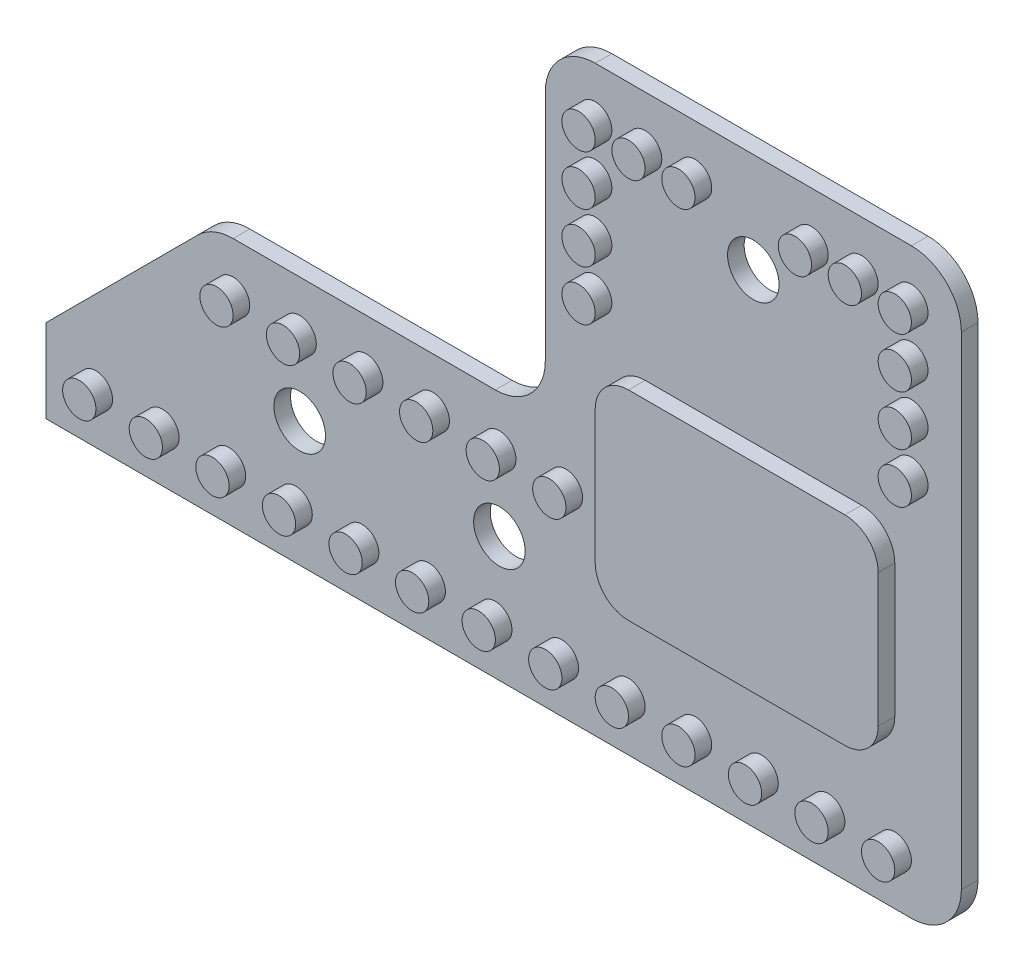
SolidWorks part; units mm, degrees
ref_plane "Front Plane" through (0, 0, 0) normal (0, 0, 1) x (1, 0, 0)
ref_plane "Top Plane" through (0, 0, 0) normal (0, 1, 0) x (1, 0, 0)
ref_plane "Right Plane" through (0, 0, 0) normal (1, 0, 0) x (0, 0, -1)
sketch "Sketch1" plane through (0, 0, 0) normal (0, 0, 1) x (1, 0, 0)
  line L0 (-36, 29) -> (-36, 12) construction
  line L1 (-41, 3) -> (-96, 3)
  line L2 (-41, 3) -> (-41, 38)
  line L3 (-41, 38) -> (-96, 38)
  line L4 (-96, 3) -> (-96, 8)
  line L5 (-40, 43) -> (-50, 43) construction
  line L6 (-96, 8) -> (-86, 18)
  line L7 (-96, 38) -> (-66, 38)
  line L8 (-96, 38) -> (-96, 18)
  line L9 (-86, 18) -> (-66, 18)
  line L10 (-66, 38) -> (-66, 18)
  line L11 (-47, 11) -> (-60, 11)
  line L12 (-45, 13) -> (-45, 21)
  line L13 (-47, 23) -> (-60, 23)
  line L14 (-62, 13) -> (-62, 21)
  line L15 (-80.7574, 15) -> (-80.7574, 6) construction
  arc A0 (-47, 23) -> (-45, 21) centre (-47, 21) cw
  arc A1 (-47, 11) -> (-45, 13) centre (-47, 13) ccw
  arc A2 (-62, 13) -> (-60, 11) centre (-60, 13) ccw
  arc A3 (-62, 21) -> (-60, 23) centre (-60, 21) cw
  circle A4 centre (-63, 35) radius 1
  circle A5 centre (-44, 35) radius 1
  circle A6 centre (-47, 35) radius 1
  circle A7 centre (-50, 35) radius 1
  circle A8 centre (-44, 32) radius 1
  circle A9 centre (-44, 29) radius 1
  circle A10 centre (-44, 26) radius 1
  circle A11 centre (-60, 35) radius 1
  circle A12 centre (-57, 35) radius 1
  circle A13 centre (-63, 32) radius 1
  circle A14 centre (-63, 29) radius 1
  circle A15 centre (-63, 26) radius 1
  circle A16 centre (-84.7574, 15) radius 1
  circle A17 centre (-80.7574, 15) radius 1
  circle A18 centre (-76.7574, 15) radius 1
  circle A19 centre (-72.7574, 15) radius 1
  circle A20 centre (-68.7574, 15) radius 1
  circle A21 centre (-64.7574, 15) radius 1
  circle A22 centre (-93, 6) radius 1
  circle A23 centre (-89, 6) radius 1
  circle A24 centre (-85, 6) radius 1
  circle A25 centre (-81, 6) radius 1
  circle A26 centre (-77, 6) radius 1
  circle A27 centre (-73, 6) radius 1
  circle A28 centre (-69, 6) radius 1
  circle A29 centre (-65, 6) radius 1
  circle A30 centre (-61, 6) radius 1
  circle A31 centre (-57, 6) radius 1
  circle A32 centre (-53, 6) radius 1
  circle A33 centre (-49, 6) radius 1
  circle A34 centre (-45, 6) radius 1
  circle A35 centre (-80.7574, 10.5) radius 1.55
  circle A36 centre (-68.7574, 10.5) radius 1.55
  circle A37 centre (-53.5, 32) radius 1.55
  dimension "D11" = 2
  dimension "D12" = 2
  dimension "D15" = 2
  dimension "D21" = 2
  dimension "D25" = 6
  dimension "D26" = 2
  dimension "D30" = 3.1
  dimension "D31" = 3.1
  dimension "D32" = 3.1
  dimension "D1" = 5
  dimension "D2" = 5
  dimension "D3" = 35
  dimension "D4" = 55
  dimension "D5" = 20
  dimension "D6" = 30
  dimension "D7" = 15
  dimension "D8" = 4
  dimension "D9" = 4
  dimension "D10" = 8
  dimension "D13" = 3
  dimension "D14" = 3
  dimension "D16" = 3
  dimension "D22" = 3
  dimension "D24" = 3
  dimension "D27" = 3
  dimension "D28" = 3
  dimension "D17" = 3
  dimension "D18" = 4
  dimension "D19" = 3
  dimension "D20" = 4
  dimension "D29" = 13
extrude "Boss-Extrude1" add sketch "Sketch1" along normal blind 1
sketch "Sketch2" plane through (0, 0, 1) normal (0, 0, 1) x (1, 0, 0)
  line L0 (-96, 38) -> (-96, 18) construction
  line L1 (-41, 38) -> (-96, 38) construction
  line L2 (-41, 3) -> (-41, 38) construction
  line L3 (-41, 3) -> (-96, 3) construction
  line L4 (-96, 3) -> (-96, 8) construction
  line L5 (-96, 8) -> (-86, 18) construction
  line L6 (-86, 18) -> (-66, 18) construction
  line L7 (-66, 38) -> (-66, 18) construction
  line L8 (-96, 38) -> (-66, 38) construction
  line L9 (-47, 11) -> (-60, 11) construction
  line L10 (-62, 13) -> (-62, 21) construction
  line L11 (-47, 23) -> (-60, 23) construction
  line L12 (-45, 13) -> (-45, 21) construction
  line L13 (-96, 38) -> (-96, 18)
  line L14 (-41, 38) -> (-96, 38)
  line L15 (-41, 3) -> (-41, 38)
  line L16 (-41, 3) -> (-96, 3)
  line L17 (-96, 3) -> (-96, 8)
  line L18 (-96, 8) -> (-86, 18)
  line L19 (-86, 18) -> (-66, 18)
  line L20 (-66, 38) -> (-66, 18)
  line L21 (-96, 38) -> (-66, 38)
  line L22 (-47, 11) -> (-60, 11)
  line L23 (-62, 13) -> (-62, 21)
  line L24 (-47, 23) -> (-60, 23)
  line L25 (-45, 13) -> (-45, 21)
  circle A0 centre (-50, 35) radius 1 construction
  circle A1 centre (-47, 35) radius 1 construction
  circle A2 centre (-44, 35) radius 1 construction
  circle A3 centre (-63, 35) radius 1 construction
  arc A4 (-62, 13) -> (-60, 11) centre (-60, 13) ccw construction
  arc A5 (-60, 23) -> (-62, 21) centre (-60, 21) ccw construction
  arc A6 (-45, 21) -> (-47, 23) centre (-47, 21) ccw construction
  arc A7 (-47, 11) -> (-45, 13) centre (-47, 13) ccw construction
  circle A8 centre (-63, 26) radius 1 construction
  circle A9 centre (-63, 29) radius 1 construction
  circle A10 centre (-63, 32) radius 1 construction
  circle A11 centre (-57, 35) radius 1 construction
  circle A12 centre (-60, 35) radius 1 construction
  circle A13 centre (-44, 26) radius 1 construction
  circle A14 centre (-44, 29) radius 1 construction
  circle A15 centre (-44, 32) radius 1 construction
  circle A16 centre (-93, 6) radius 1 construction
  circle A17 centre (-64.7574, 15) radius 1 construction
  circle A18 centre (-68.7574, 15) radius 1 construction
  circle A19 centre (-72.7574, 15) radius 1 construction
  circle A20 centre (-76.7574, 15) radius 1 construction
  circle A21 centre (-80.7574, 15) radius 1 construction
  circle A22 centre (-84.7574, 15) radius 1 construction
  circle A23 centre (-65, 6) radius 1 construction
  circle A24 centre (-69, 6) radius 1 construction
  circle A25 centre (-73, 6) radius 1 construction
  circle A26 centre (-77, 6) radius 1 construction
  circle A27 centre (-81, 6) radius 1 construction
  circle A28 centre (-85, 6) radius 1 construction
  circle A29 centre (-89, 6) radius 1 construction
  circle A30 centre (-53.5, 32) radius 1.55 construction
  circle A31 centre (-68.7574, 10.5) radius 1.55 construction
  circle A32 centre (-80.7574, 10.5) radius 1.55 construction
  circle A33 centre (-45, 6) radius 1 construction
  circle A34 centre (-49, 6) radius 1 construction
  circle A35 centre (-53, 6) radius 1 construction
  circle A36 centre (-57, 6) radius 1 construction
  circle A37 centre (-61, 6) radius 1 construction
  circle A38 centre (-50, 35) radius 1
  circle A39 centre (-47, 35) radius 1
  circle A40 centre (-44, 35) radius 1
  circle A41 centre (-63, 35) radius 1
  arc A42 (-62, 13) -> (-60, 11) centre (-60, 13) ccw
  arc A43 (-60, 23) -> (-62, 21) centre (-60, 21) ccw
  arc A44 (-45, 21) -> (-47, 23) centre (-47, 21) ccw
  arc A45 (-47, 11) -> (-45, 13) centre (-47, 13) ccw
  circle A46 centre (-63, 26) radius 1
  circle A47 centre (-63, 29) radius 1
  circle A48 centre (-63, 32) radius 1
  circle A49 centre (-57, 35) radius 1
  circle A50 centre (-60, 35) radius 1
  circle A51 centre (-44, 26) radius 1
  circle A52 centre (-44, 29) radius 1
  circle A53 centre (-44, 32) radius 1
  circle A54 centre (-93, 6) radius 1
  circle A55 centre (-64.7574, 15) radius 1
  circle A56 centre (-68.7574, 15) radius 1
  circle A57 centre (-72.7574, 15) radius 1
  circle A58 centre (-76.7574, 15) radius 1
  circle A59 centre (-80.7574, 15) radius 1
  circle A60 centre (-84.7574, 15) radius 1
  circle A61 centre (-65, 6) radius 1
  circle A62 centre (-69, 6) radius 1
  circle A63 centre (-73, 6) radius 1
  circle A64 centre (-77, 6) radius 1
  circle A65 centre (-81, 6) radius 1
  circle A66 centre (-85, 6) radius 1
  circle A67 centre (-89, 6) radius 1
  circle A68 centre (-53.5, 32) radius 1.55
  circle A69 centre (-68.7574, 10.5) radius 1.55
  circle A70 centre (-80.7574, 10.5) radius 1.55
  circle A71 centre (-45, 6) radius 1
  circle A72 centre (-49, 6) radius 1
  circle A73 centre (-53, 6) radius 1
  circle A74 centre (-57, 6) radius 1
  circle A75 centre (-61, 6) radius 1
extrude "Boss-Extrude2" add sketch "Sketch2" along normal blind 1 contours L22 A45 L25 A44 L24 A43 L23 A42 | A46 | A47 | A48 | A41 | A50 | A49 | A38 | A39 | A53 | A52 | A51 | A71 | A72 | A73 | A74 | A75 | A61 | A62 | A63 | A64 | A65 | A66 | A67 | A54 | A60 | A58 | A57 | A56 | A55 | A40 | A59
fillet "Fillet1" radius 3 5 edges at (-86, 18, 0.5) (-41, 3, 0.5) (-41, 38, 0.5) (-66, 18, 0.5) (-66, 38, 0.5)
sketch "Sketch3" plane through (0, 0, 1) normal (0, 0, 1) x (1, 0, 0)
  line L0 (-96, 38) -> (-96, 18) construction
  line L1 (-41, 38) -> (-96, 38) construction
  line L2 (-41, 3) -> (-41, 38) construction
  line L3 (-41, 3) -> (-96, 3) construction
  line L4 (-96, 3) -> (-96, 8) construction
  line L5 (-96, 8) -> (-86, 18) construction
  line L6 (-86, 18) -> (-66, 18) construction
  line L7 (-66, 38) -> (-66, 18) construction
  line L8 (-96, 38) -> (-66, 38) construction
  line L9 (-47, 11) -> (-60, 11) construction
  line L10 (-62, 13) -> (-62, 21) construction
  line L11 (-47, 23) -> (-60, 23) construction
  line L12 (-45, 13) -> (-45, 21) construction
  line L13 (-96, 38) -> (-96, 18)
  line L14 (-41, 38) -> (-96, 38)
  line L15 (-41, 3) -> (-41, 38)
  line L16 (-41, 3) -> (-96, 3)
  line L17 (-96, 3) -> (-96, 8)
  line L18 (-96, 8) -> (-86, 18)
  line L19 (-86, 18) -> (-66, 18)
  line L20 (-66, 38) -> (-66, 18)
  line L21 (-96, 38) -> (-66, 38)
  line L22 (-47, 11) -> (-60, 11)
  line L23 (-62, 13) -> (-62, 21)
  line L24 (-47, 23) -> (-60, 23)
  line L25 (-45, 13) -> (-45, 21)
  arc A0 (-62, 13) -> (-60, 11) centre (-60, 13) ccw construction
  arc A1 (-60, 23) -> (-62, 21) centre (-60, 21) ccw construction
  arc A2 (-45, 21) -> (-47, 23) centre (-47, 21) ccw construction
  arc A3 (-47, 11) -> (-45, 13) centre (-47, 13) ccw construction
  circle A4 centre (-63, 32) radius 1 construction
  circle A5 centre (-63, 29) radius 1 construction
  circle A6 centre (-63, 26) radius 1 construction
  circle A7 centre (-63, 35) radius 1 construction
  circle A8 centre (-44, 35) radius 1 construction
  circle A9 centre (-47, 35) radius 1 construction
  circle A10 centre (-50, 35) radius 1 construction
  circle A11 centre (-77, 6) radius 1 construction
  circle A12 centre (-73, 6) radius 1 construction
  circle A13 centre (-69, 6) radius 1 construction
  circle A14 centre (-65, 6) radius 1 construction
  circle A15 centre (-84.7574, 15) radius 1 construction
  circle A16 centre (-80.7574, 15) radius 1 construction
  circle A17 centre (-76.7574, 15) radius 1 construction
  circle A18 centre (-72.7574, 15) radius 1 construction
  circle A19 centre (-68.7574, 15) radius 1 construction
  circle A20 centre (-64.7574, 15) radius 1 construction
  circle A21 centre (-93, 6) radius 1 construction
  circle A22 centre (-44, 32) radius 1 construction
  circle A23 centre (-44, 29) radius 1 construction
  circle A24 centre (-44, 26) radius 1 construction
  circle A25 centre (-60, 35) radius 1 construction
  circle A26 centre (-57, 35) radius 1 construction
  circle A27 centre (-61, 6) radius 1 construction
  circle A28 centre (-57, 6) radius 1 construction
  circle A29 centre (-53, 6) radius 1 construction
  circle A30 centre (-49, 6) radius 1 construction
  circle A31 centre (-45, 6) radius 1 construction
  circle A32 centre (-80.7574, 10.5) radius 1.55 construction
  circle A33 centre (-68.7574, 10.5) radius 1.55 construction
  circle A34 centre (-53.5, 32) radius 1.55 construction
  circle A35 centre (-89, 6) radius 1 construction
  circle A36 centre (-85, 6) radius 1 construction
  circle A37 centre (-81, 6) radius 1 construction
  arc A38 (-62, 13) -> (-60, 11) centre (-60, 13) ccw
  arc A39 (-60, 23) -> (-62, 21) centre (-60, 21) ccw
  arc A40 (-45, 21) -> (-47, 23) centre (-47, 21) ccw
  arc A41 (-47, 11) -> (-45, 13) centre (-47, 13) ccw
  circle A42 centre (-63, 32) radius 1
  circle A43 centre (-63, 29) radius 1
  circle A44 centre (-63, 26) radius 1
  circle A45 centre (-63, 35) radius 1
  circle A46 centre (-44, 35) radius 1
  circle A47 centre (-47, 35) radius 1
  circle A48 centre (-50, 35) radius 1
  circle A49 centre (-77, 6) radius 1
  circle A50 centre (-73, 6) radius 1
  circle A51 centre (-69, 6) radius 1
  circle A52 centre (-65, 6) radius 1
  circle A53 centre (-84.7574, 15) radius 1
  circle A54 centre (-80.7574, 15) radius 1
  circle A55 centre (-76.7574, 15) radius 1
  circle A56 centre (-72.7574, 15) radius 1
  circle A57 centre (-68.7574, 15) radius 1
  circle A58 centre (-64.7574, 15) radius 1
  circle A59 centre (-93, 6) radius 1
  circle A60 centre (-44, 32) radius 1
  circle A61 centre (-44, 29) radius 1
  circle A62 centre (-44, 26) radius 1
  circle A63 centre (-60, 35) radius 1
  circle A64 centre (-57, 35) radius 1
  circle A65 centre (-61, 6) radius 1
  circle A66 centre (-57, 6) radius 1
  circle A67 centre (-53, 6) radius 1
  circle A68 centre (-49, 6) radius 1
  circle A69 centre (-45, 6) radius 1
  circle A70 centre (-80.7574, 10.5) radius 1.55
  circle A71 centre (-68.7574, 10.5) radius 1.55
  circle A72 centre (-53.5, 32) radius 1.55
  circle A73 centre (-89, 6) radius 1
  circle A74 centre (-85, 6) radius 1
  circle A75 centre (-81, 6) radius 1
extrude "Cut-Extrude1" cut sketch "Sketch3" against normal up to next contours A72 | A71 | A70
